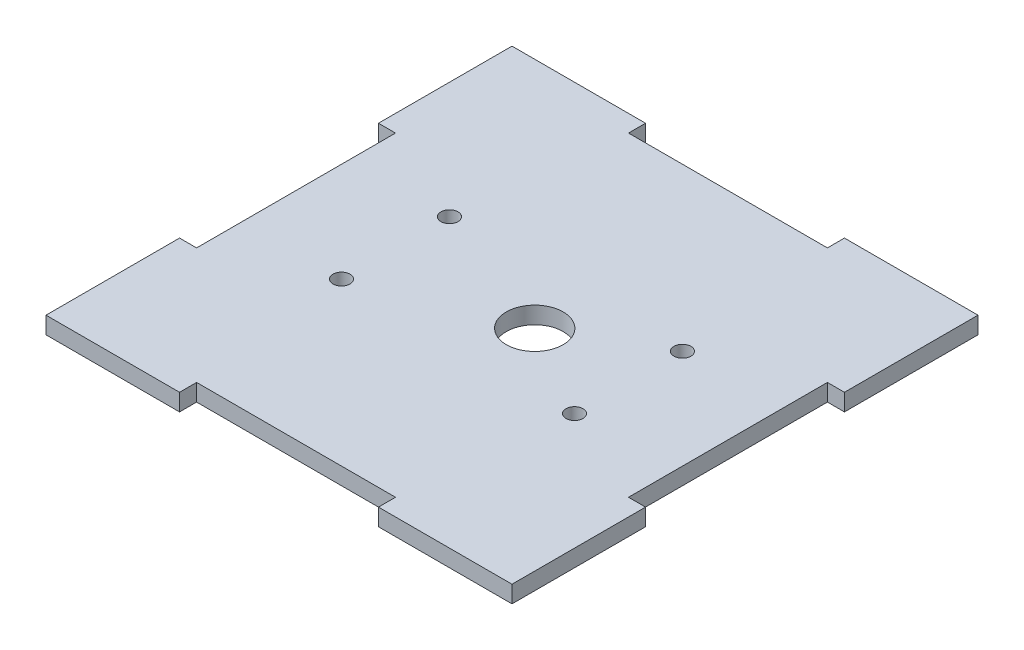
SolidWorks part; units mm, degrees
ref_plane "Front Plane" through (0, 0, 0) normal (0, 0, 1) x (1, 0, 0)
ref_plane "Top Plane" through (0, 0, 0) normal (0, 1, 0) x (1, 0, 0)
ref_plane "Right Plane" through (0, 0, 0) normal (1, 0, 0) x (0, 0, -1)
sketch "Sketch1" plane through (0, 0, 0) normal (0, 1, 0) x (1, 0, 0)
  line L0 (0, 38) -> (0, -38) construction
  line L1 (-41, -41) -> (-17.5, -41)
  line L2 (-41, -41) -> (-41, -17.5)
  line L3 (-41, 41) -> (-17.5, 41)
  line L4 (41, -41) -> (41, -17.5)
  line L5 (-41, -41) -> (41, 41) construction
  line L6 (-41, 41) -> (41, -41) construction
  line L11 (-41, 17.5) -> (-38, 17.5)
  line L12 (-38, 17.5) -> (-38, -17.5)
  line L13 (-35, 0) -> (38, 0) construction
  line L26 (17.5, 41) -> (41, 41)
  line L27 (41, 17.5) -> (41, 41)
  line L28 (17.5, -41) -> (41, -41)
  line L29 (-41, 17.5) -> (-41, 41)
  line L30 (-38, -17.5) -> (-41, -17.5)
  line L31 (-17.5, 41) -> (-17.5, 38)
  line L32 (-17.5, 38) -> (17.5, 38)
  line L33 (17.5, 38) -> (17.5, 41)
  line L34 (41, 17.5) -> (38, 17.5)
  line L35 (38, 17.5) -> (38, -17.5)
  line L36 (38, -17.5) -> (41, -17.5)
  line L37 (17.5, -41) -> (17.5, -38)
  line L38 (17.5, -38) -> (-17.5, -38)
  line L39 (-17.5, -38) -> (-17.5, -41)
  point P0 (0, 0)
  point P6 (0, 0)
  dimension "D1" = 3
  dimension "D2" = 82
  dimension "D3" = 3
  dimension "D4" = 82
  dimension "D5" = 3
  dimension "D6" = 3
extrude "Boss-Extrude1" add sketch "Sketch1" along normal blind 3
sketch "Sketch2" plane through (0, 3, 0) normal (0, 1, 0) x (1, 0, 0)
  line L0 (0, 12) -> (0, -12) construction
  line L5 (-23, -12) -> (23, -12) construction
  line L6 (-23, -12) -> (-23, 12) construction
  line L7 (-23, 12) -> (23, 12) construction
  line L8 (23, -12) -> (23, 12) construction
  line L9 (-23, -12) -> (23, 12) construction
  line L10 (-23, 12) -> (23, -12) construction
  line L11 (-23, 0) -> (23, 0) construction
  circle A1 centre (4, 0) radius 5
  circle A2 centre (-20.5, 9.5) radius 1.5
  circle A3 centre (-20.5, -9.5) radius 1.5
  circle A4 centre (20.5, -9.5) radius 1.5
  circle A5 centre (20.5, 9.5) radius 1.5
  point P0 (0, 0)
  dimension "D3" = 10
  dimension "D4" = 3
  dimension "D1" = 46
  dimension "D2" = 24
  dimension "D5" = 12
  dimension "D6" = 19
  dimension "D7" = 2.5
  dimension "D8" = 2.5
extrude "Cut-Extrude1" cut sketch "Sketch2" against normal blind 3
